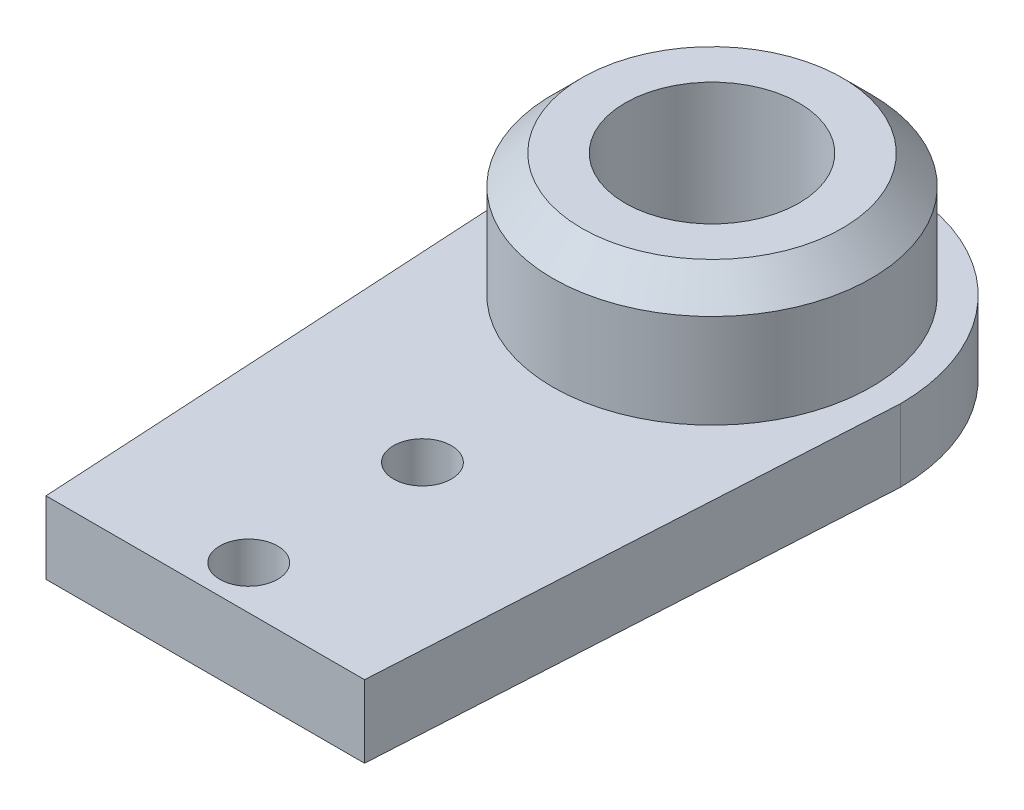
SolidWorks part; units mm, degrees
ref_plane "Front Plane" through (0, 0, 0) normal (0, 0, 1) x (1, 0, 0)
ref_plane "Top Plane" through (0, 0, 0) normal (0, 1, 0) x (1, 0, 0)
ref_plane "Right Plane" through (0, 0, 0) normal (1, 0, 0) x (0, 0, -1)
sketch "Sketch1" plane through (0, 0, 0) normal (0, 1, 0) x (1, 0, 0)
  line L0 (-6.5, 0) -> (-5.5, -17.5)
  line L1 (-5.5, -17.5) -> (5.5, -17.5)
  line L2 (5.5, -17.5) -> (6.5, 0)
  arc A0 (6.4577, -0.7404) -> (-6.4577, -0.7404) centre (0, 0) ccw
  circle A1 centre (0, -10) radius 1
  circle A2 centre (0, -16) radius 1
  dimension "D1" = 13
  dimension "D2" = 24
  dimension "D5" = 2
  dimension "D6" = 2
  dimension "D7" = 3.5
  dimension "D3" = 11
  dimension "D4" = 13
  dimension "D8" = 6
extrude "Boss-Extrude1" add sketch "Sketch1" along normal blind 2.5 contours L2 A0 L0 L1 A2 A1
sketch "Sketch2" plane through (0, 2.5, 0) normal (0, 1, 0) x (1, 0, 0)
  circle A0 centre (0, 0) radius 5.5
  circle A1 centre (0, 0) radius 3
  dimension "D1" = 11
  dimension "D2" = 6
extrude "Boss-Extrude3" add sketch "Sketch2" along normal blind 4.25
sketch "Sketch4" plane through (0, 2.5, 0) normal (0, 1, 0) x (1, 0, 0)
  circle A0 centre (0, 0) radius 3
extrude "Cut-Extrude1" cut sketch "Sketch4" against normal up to next
chamfer "Chamfer1" distance 1 angle 45 1 edges at (0, 6.75, 5.5)
